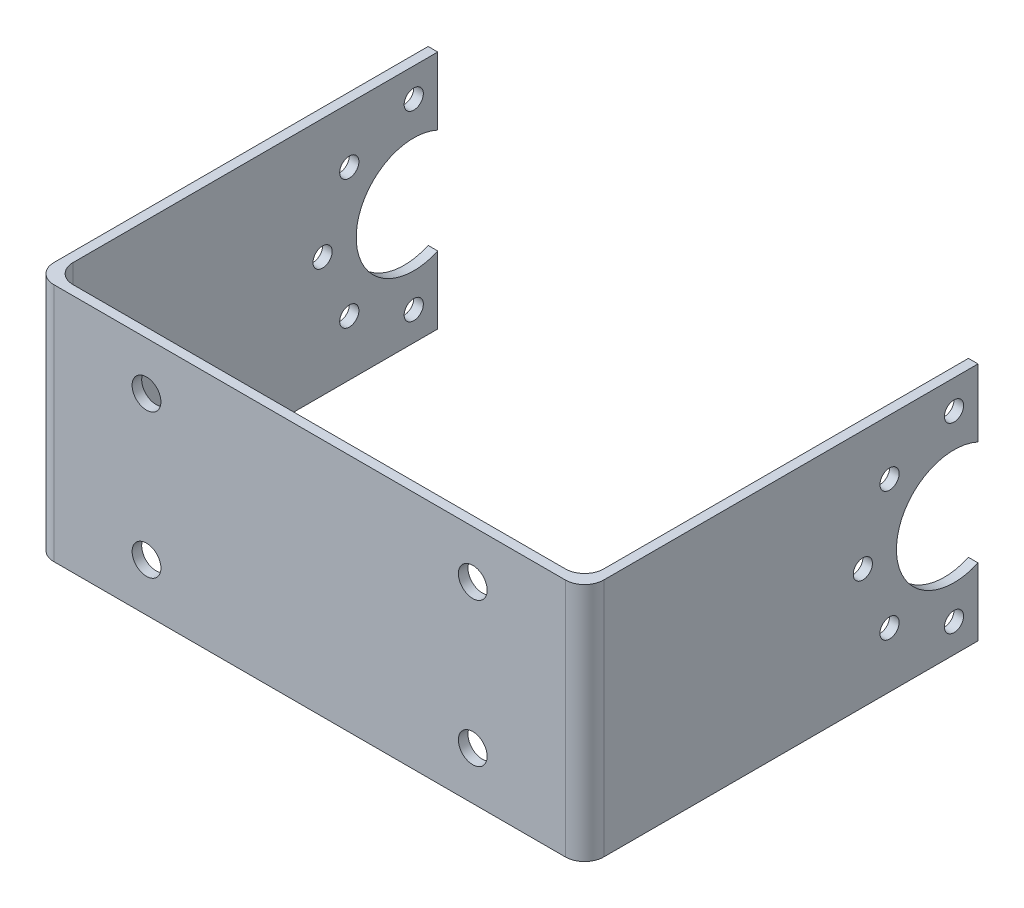
SolidWorks part; units mm, degrees
material "1060 Alloy"
ref_plane "Front Plane" through (0, 0, 0) normal (0, 0, 1) x (1, 0, 0)
ref_plane "Top Plane" through (0, 0, 0) normal (0, 1, 0) x (1, 0, 0)
ref_plane "Right Plane" through (0, 0, 0) normal (1, 0, 0) x (0, 0, -1)
sketch "Sketch1" plane through (0, 0, 0) normal (0, 1, 0) x (1, 0, 0)
  line L1 (-21.5, 0.5) -> (33.8, 0.5)
  line L2 (-22.5, 0.5) -> (-22.5, -0.5)
  line L3 (-22.5, -0.5) -> (34.8, -0.5)
  line L4 (34.8, 0.5) -> (34.8, -0.5)
  line L8 (34.8, 0.5) -> (34.8, 40.5)
  line L9 (34.8, 40.5) -> (33.8, 40.5)
  line L10 (33.8, 0.5) -> (33.8, 40.5)
  line L12 (-22.5, 0.5) -> (-22.5, 40.5)
  line L13 (-22.5, 40.5) -> (-21.5, 40.5)
  line L14 (-21.5, 0.5) -> (-21.5, 40.5)
  point P0 (0, 0)
  dimension "D1" = 57.3
  dimension "D2" = 1
  dimension "D3" = 1
  dimension "D4" = 1
  dimension "D5" = 40
  dimension "D6" = 40
extrude "Boss-Extrude1" add sketch "Sketch1" along normal blind 25
sketch "Sketch2" plane through (34.8, 0, 0) normal (1, 0, 0) x (0, 0, -1)
  line L1 (40.5, 12.5) -> (38, 12.5)
  line L2 (40.5, 25) -> (40.5, 0) construction
  line L3 (32, 12.5) -> (28.5, 12.5)
  circle A0 centre (38, 12.5) radius 6
  circle A1 centre (28.5, 12.5) radius 1
  circle A2 centre (31.2825, 19.2175) radius 1
  circle A3 centre (38, 22) radius 1
  circle A4 centre (44.7175, 19.2175) radius 1
  circle A5 centre (47.5, 12.5) radius 1
  circle A6 centre (44.7175, 5.7825) radius 1
  circle A7 centre (38, 3) radius 1
  circle A8 centre (31.2825, 5.7825) radius 1
  point P25 (38, 12.5)
  dimension "D1" = 2.5
  dimension "D3" = 3.5
  dimension "D2" = 12
  dimension "D4" = 2
  dimension "D5" = 8
extrude "Cut-Extrude1" cut sketch "Sketch2" against normal through all
fillet "Fillet2" radius 2 4 edges at (-22.5, 12.5, 0.5) (-21.5, 12.5, -0.5) (34.8, 12.5, 0.5) (33.8, 12.5, -0.5)
sketch "Sketch3" plane through (0, 0, 0.5) normal (0, 0, 1) x (1, 0, 0)
  line L0 (6.15, 25) -> (6.15, 20)
  line L2 (6.15, 20) -> (-10.85, 20)
  line L3 (6.15, 20) -> (23.15, 20)
  line L4 (-20.5, 25) -> (32.8, 25) construction
  line L5 (6.15, 0) -> (6.15, 5)
  line L6 (-20.5, 0) -> (32.8, 0) construction
  line L8 (6.15, 5) -> (-10.85, 5)
  line L9 (6.15, 5) -> (23.15, 5)
  circle A0 centre (-10.85, 20) radius 1.5
  circle A1 centre (23.15, 20) radius 1.5
  circle A2 centre (-10.85, 5) radius 1.5
  circle A3 centre (23.15, 5) radius 1.5
  dimension "D3" = 3
  dimension "D4" = 3
  dimension "D9" = 3
  dimension "D10" = 3
  dimension "D1" = 17
  dimension "D2" = 17
  dimension "D5" = 5
  dimension "D6" = 5
  dimension "D7" = 17
  dimension "D8" = 17
extrude "Cut-Extrude2" cut sketch "Sketch3" against normal through all
